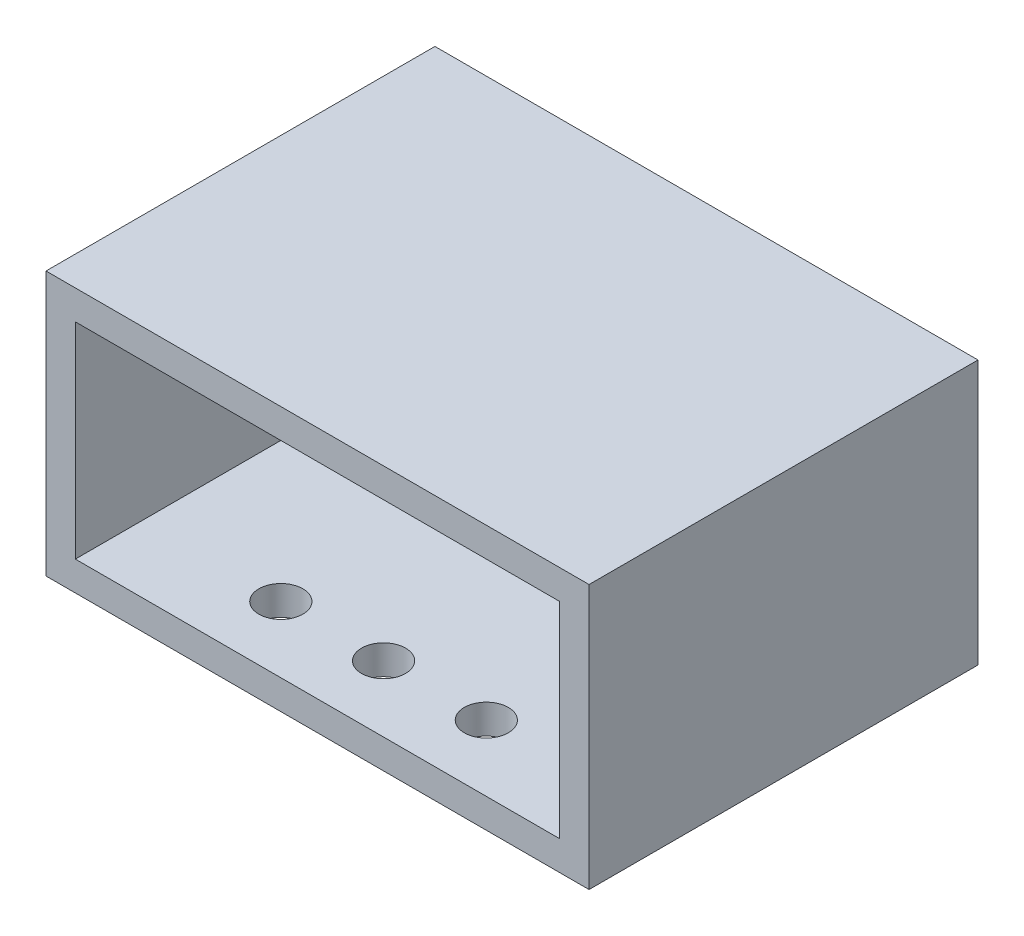
SolidWorks part; units mm, degrees
ref_plane "Ebene vorne" through (0, 0, 0) normal (0, 0, 1) x (1, 0, 0)
ref_plane "Ebene oben" through (0, 0, 0) normal (0, 1, 0) x (1, 0, 0)
ref_plane "Ebene rechts" through (0, 0, 0) normal (1, 0, 0) x (0, 0, -1)
sketch "Skizze1" plane through (0, 0, 0) normal (0, 1, 0) x (1, 0, 0)
  line L1 (-18.5, -13.25) -> (18.5, -13.25)
  line L2 (-18.5, -13.25) -> (-18.5, 13.25)
  line L3 (-18.5, 13.25) -> (18.5, 13.25)
  line L4 (18.5, -13.25) -> (18.5, 13.25)
  line L5 (-18.5, -13.25) -> (18.5, 13.25) construction
  line L6 (-18.5, 13.25) -> (18.5, -13.25) construction
  point P0 (0, 0)
  point P1 (0, 0)
  dimension "D1" = 26.5
  dimension "D2" = 37
extrude "Aufsatz-Linear austragen1" add sketch "Skizze1" along normal blind 18
ref_plane "Ebene1" through (0, 0, -11.25) normal (0, 0, -1) x (-1, 0, 0)
sketch "Skizze5" plane through (0, 0, -11.25) normal (0, 0, -1) x (-1, 0, 0)
  line L0 (18.5, 18) -> (-18.5, 0) construction
  line L1 (18.5, 0) -> (-18.5, 18) construction
  line L2 (18.5, 18) -> (18.5, 0) construction
  line L3 (-16.5, 2) -> (16.5, 2)
  line L4 (-16.5, 2) -> (-16.5, 16)
  line L5 (-16.5, 16) -> (16.5, 16)
  line L6 (16.5, 2) -> (16.5, 16)
  line L7 (-16.5, 2) -> (16.5, 16) construction
  line L8 (-16.5, 16) -> (16.5, 2) construction
  line L9 (18.5, 18) -> (-18.5, 18) construction
  point P0 (18.5, 0)
  point P1 (18.5, 18)
  point P3 (-18.5, 18)
  point P5 (-18.5, 0)
  point P12 (0, 9)
  point P13 (0, 9)
  dimension "D1" = 2
  dimension "D2" = 2
extrude "Schnitt-Linear austragen1" cut sketch "Skizze5" against normal blind 28
sketch "Skizze6" plane through (0, 0, 0) normal (0, -1, 0) x (1, 0, 0)
  line L0 (-7, 8.75) -> (-7, 13.25) construction
  line L1 (-18.5, 13.25) -> (18.5, 13.25) construction
  line L2 (7, 8.75) -> (7, 13.25) construction
  line L3 (-8.5, 8.75) -> (-18.5, 8.75) construction
  line L4 (-18.5, -13.25) -> (-18.5, 13.25) construction
  line L5 (-8.5, 8.75) -> (-5.5, 8.75) construction
  line L6 (-5.5, 8.75) -> (-1.5, 8.75) construction
  line L7 (-1.5, 8.75) -> (1.5, 8.75) construction
  line L8 (1.5, 8.75) -> (5.5, 8.75) construction
  line L9 (5.5, 8.75) -> (8.5, 8.75) construction
  line L10 (8.5, 8.75) -> (18.5, 8.75) construction
  line L11 (18.5, 13.25) -> (18.5, -13.25) construction
  line L12 (0, 8.75) -> (0, 13.25) construction
  circle A0 centre (-7, 8.75) radius 1.5
  circle A1 centre (7, 8.75) radius 1.5
  circle A2 centre (0, 8.75) radius 1.5
  point P4 (-18.5, 13.25)
  point P5 (18.5, 13.25)
  point P18 (0, 0)
  dimension "D1" = 3
  dimension "D2" = 3
  dimension "D3" = 3
  dimension "D4" = 4.5
  dimension "D5" = 4
extrude "Schnitt-Linear austragen2" cut sketch "Skizze6" against normal mid plane 8
mirror "Spiegeln1" about plane through (0, 0, 0) normal (0, 0, 1) of "Schnitt-Linear austragen2"
